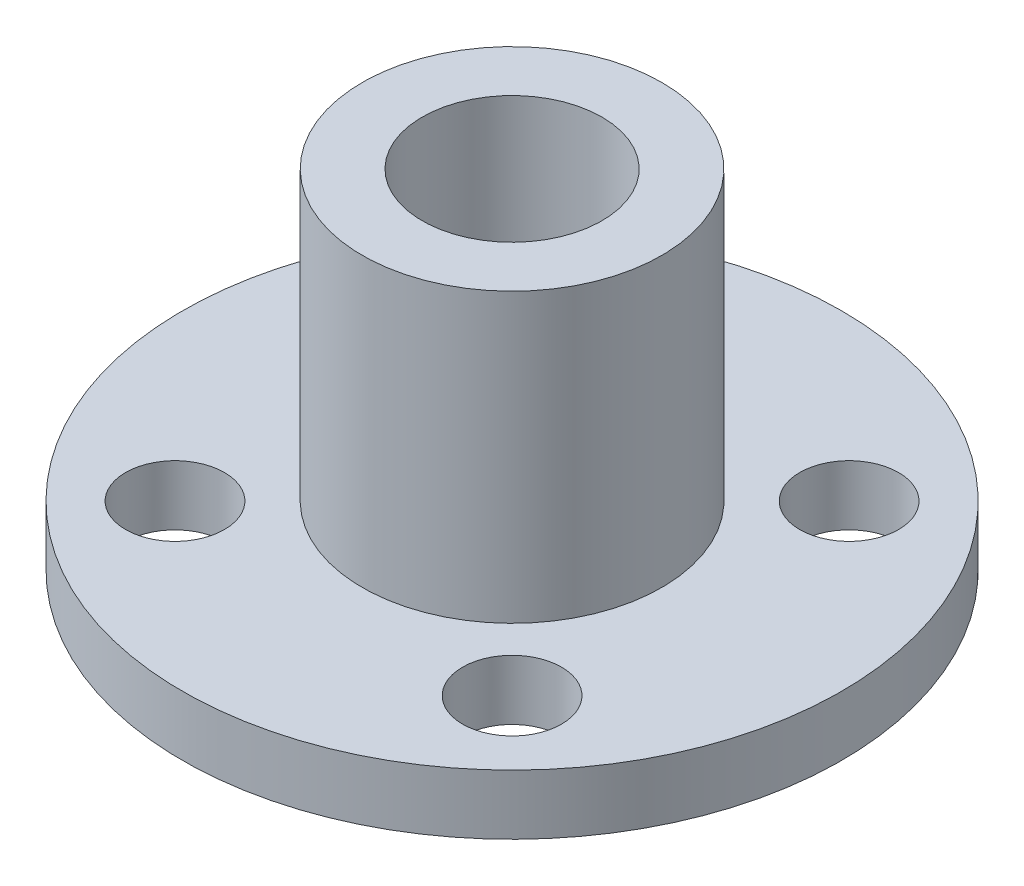
SolidWorks part; units mm, degrees
ref_plane "前视基准面" through (0, 0, 0) normal (0, 0, 1) x (1, 0, 0)
ref_plane "上视基准面" through (0, 0, 0) normal (0, 1, 0) x (1, 0, 0)
ref_plane "右视基准面" through (0, 0, 0) normal (1, 0, 0) x (0, 0, -1)
sketch "草图2" plane through (0, 0, 0) normal (0, 0, 1) x (1, 0, 0)
  line L0 (3, 11.6) -> (3, 0)
  line L1 (3, 0) -> (11, 0)
  line L2 (11, 0) -> (11, 2)
  line L3 (11, 2) -> (5, 2)
  line L4 (5, 2) -> (5, 11.6)
  line L5 (5, 11.6) -> (3, 11.6)
  line L6 (0, 0) -> (0, 16.0714) construction
  dimension "D1" = 11
  dimension "D2" = 5
  dimension "D3" = 3
  dimension "D4" = 11.6
  dimension "D5" = 2
revolve "旋转1" add sketch "草图2" angle 360 about L6
sketch "草图3" plane through (0, 0, 0) normal (0, -1, 0) x (1, 0, 0)
  line L1 (-5.625, -5.625) -> (5.625, -5.625) construction
  line L2 (-5.625, -5.625) -> (-5.625, 5.625) construction
  line L3 (-5.625, 5.625) -> (5.625, 5.625) construction
  line L4 (5.625, -5.625) -> (5.625, 5.625) construction
  line L5 (-5.625, -5.625) -> (5.625, 5.625) construction
  line L6 (-5.625, 5.625) -> (5.625, -5.625) construction
  circle A0 centre (-5.625, 5.625) radius 1.65
  circle A1 centre (5.625, 5.625) radius 1.65
  circle A2 centre (5.625, -5.625) radius 1.65
  circle A3 centre (-5.625, -5.625) radius 1.65
  point P0 (0, 0)
  dimension "D1" = 3.3
  dimension "D2" = 11.25
extrude "切除-拉伸1" cut sketch "草图3" against normal through all
